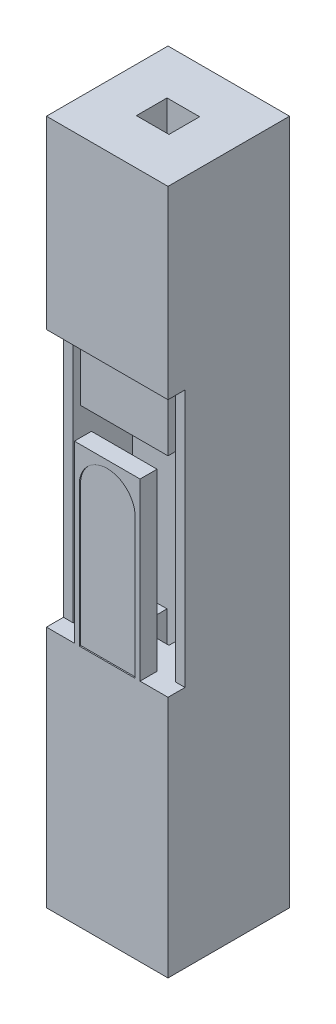
SolidWorks part; units mm, degrees
other "Camera1"
material "Nylon 101"
ref_plane "Front Plane" through (0, 0, 0) normal (0, 0, 1) x (1, 0, 0)
ref_plane "Top Plane" through (0, 0, 0) normal (0, 1, 0) x (1, 0, 0)
ref_plane "Right Plane" through (0, 0, 0) normal (1, 0, 0) x (0, 0, -1)
sketch "Sketch2" plane through (0, 0, 0) normal (0, 1, 0) x (1, 0, 0)
  line L1 (-1.25, -1.25) -> (1.25, -1.25)
  line L2 (-1.25, -1.25) -> (-1.25, 1.25)
  line L3 (-1.25, 1.25) -> (1.25, 1.25)
  line L4 (1.25, -1.25) -> (1.25, 1.25)
  line L5 (-1.25, -1.25) -> (1.25, 1.25) construction
  line L6 (-1.25, 1.25) -> (1.25, -1.25) construction
  point P0 (0, 0)
  dimension "D1" = 2.5
extrude "Boss-Extrude1" add sketch "Sketch2" along normal mid plane 14.1
sketch "Sketch3" plane through (0, 7.05, 0) normal (0, 1, 0) x (1, 0, 0)
  line L1 (0.335, -0.315) -> (-0.335, -0.315)
  line L2 (0.335, -0.315) -> (0.335, 0.315)
  line L3 (0.335, 0.315) -> (-0.335, 0.315)
  line L4 (-0.335, -0.315) -> (-0.335, 0.315)
  line L5 (0.335, -0.315) -> (-0.335, 0.315) construction
  line L6 (0.335, 0.315) -> (-0.335, -0.315) construction
  point P0 (0, 0)
  dimension "D1" = 0.63
  dimension "D2" = 0.67
extrude "Pinhole" cut sketch "Sketch3" against normal up to next
sketch "Sketch4" plane through (0, 0, 1.25) normal (0, 0, 1) x (1, 0, 0)
  line L0 (-1.25, 7.05) -> (-1.25, -7.05) construction
  line L1 (-1.25, 3.25) -> (1.25, 3.25)
  line L2 (-1.25, 3.25) -> (-1.25, -2.05)
  line L3 (-1.25, -2.05) -> (-0.675, -2.05)
  line L4 (1.25, 3.25) -> (1.25, -2.05)
  line L5 (0.675, -2.05) -> (1.25, -2.05)
  line L6 (-0.675, -2.05) -> (0.675, -2.05) construction
  line L7 (1.25, 7.05) -> (1.25, -7.05) construction
  line L8 (-1.25, 7.05) -> (1.25, 7.05) construction
  line L9 (-1.25, -7.05) -> (1.25, -7.05) construction
  line L10 (-0.675, -2.05) -> (-0.675, 1.55)
  line L11 (-0.675, 1.55) -> (0.675, 1.55)
  line L12 (0.675, -2.05) -> (0.675, 1.55)
  dimension "D1" = 3.8
  dimension "D2" = 5
  dimension "D3" = 1.35
  dimension "D4" = 3.6
extrude "Cut-Extrude2" cut sketch "Sketch4" against normal blind 0.35
sketch "Sketch5" plane through (0, 0, 0.9) normal (0, 0, 1) x (1, 0, 0)
  line L0 (-1.25, 7.05) -> (1.25, 7.05) construction
  line L1 (-1.05, 3.25) -> (1.05, 3.25)
  line L2 (-1.05, 3.25) -> (-1.05, -2.05)
  line L3 (-1.05, -2.05) -> (1.05, -2.05)
  line L4 (1.05, 3.25) -> (1.05, -2.05)
  line L5 (-1.05, 3.25) -> (1.05, -2.05) construction
  line L6 (-1.05, -2.05) -> (1.05, 3.25) construction
  line L7 (0.675, -2.05) -> (1.25, -2.05) construction
  line L8 (-1.25, 3.25) -> (-1.25, -2.05) construction
  line L9 (1.25, 3.25) -> (-1.25, 3.25) construction
  point P4 (0, 0.6)
  point P5 (0, 3.25)
  point P8 (0, 7.05)
  dimension "D1" = 0.2
extrude "Cut-Extrude3" cut sketch "Sketch5" against normal up to surface (1.215 mm away) up to face at (0, 0, -0.315)
sketch "Sketch6" plane through (0, 0, 1.25) normal (0, 0, 1) x (1, 0, 0)
  line L0 (-0.575, -2.05) -> (-0.575, 0.825)
  line L1 (-0.675, -2.05) -> (-0.675, 1.55) construction
  line L2 (-0.6925, -2.05) -> (0.6925, -2.05)
  line L3 (-1.05, -2.05) -> (-0.335, -2.05) construction
  line L4 (0.335, -2.05) -> (1.05, -2.05) construction
  line L5 (0, 1.55) -> (0, -2.05) construction
  line L6 (-0.675, 1.55) -> (0.675, 1.55) construction
  line L7 (0.575, -2.05) -> (0.575, 0.825)
  arc A0 (-0.575, 0.825) -> (0.575, 0.825) centre (0, 0.825) cw
  point P17 (0, 1.4)
  dimension "D2" = 0.15
  dimension "D1" = 0.1
extrude "Cut-Extrude5" cut sketch "Sketch6" against normal blind 0.025 contours L5 A0 L0 L2 | A0 L5 L2 L7
sketch "Sketch7" plane through (0, -7.05, 0) normal (0, -1, 0) x (1, 0, 0)
  line L0 (-1.25, -1.25) -> (-1.25, 1.25) construction
  line L1 (1.05, -1.05) -> (-1.05, -1.05)
  line L2 (1.05, -1.05) -> (1.05, 1.05)
  line L3 (1.05, 1.05) -> (-1.05, 1.05)
  line L4 (-1.05, -1.05) -> (-1.05, 1.05)
  line L5 (1.05, -1.05) -> (-1.05, 1.05) construction
  line L6 (1.05, 1.05) -> (-1.05, -1.05) construction
  point P0 (0, 0)
  dimension "D1" = 0.2
extrude "Cut-Extrude6" cut sketch "Sketch7" against normal blind 4
sketch "Sketch8" [suppressed] plane through (0, -3.05, 0) normal (0, -1, 0) x (1, 0, 0)
  circle A0 centre (0, 0) radius 0.45
  circle A1 centre (0, 0) radius 0.55
  dimension "D1" = 0.9
  dimension "D2" = 0.1
extrude "Wire hole" [suppressed] add sketch "Sketch8" along normal blind 3
sketch "Sketch9" plane through (0, 0, -0.315) normal (0, 0, 1) x (1, 0, 0)
  line L1 (-0.9, 2.9) -> (-0.75, 2.9)
  line L2 (-0.9, 2.9) -> (-0.9, 1.9)
  line L3 (-0.9, 1.9) -> (-0.75, 1.9)
  line L4 (0.9, 2.9) -> (0.9, 1.9)
  line L5 (0.75, 2.9) -> (-0.75, 2.9) construction
  line L6 (0.9, 2.9) -> (0.75, 2.9)
  line L7 (-0.335, 3.25) -> (0.335, 3.25) construction
  line L8 (-0.75, 2.9) -> (-0.75, 1.9)
  line L9 (0, 2.9) -> (0, 1.9) construction
  line L10 (0.75, 2.9) -> (0.75, 1.9)
  line L11 (-1.05, 3.25) -> (-1.05, -2.05) construction
  line L12 (0, 3.25) -> (0, 2.9) construction
  line L13 (0.75, 1.9) -> (-0.75, 1.9) construction
  line L14 (0.75, 1.9) -> (0.9, 1.9)
  point P4 (0, 2.4)
  point P23 (0, 2.9)
  point P24 (0, 1.9)
  dimension "D1" = 1
  dimension "D2" = 0.15
  dimension "D3" = 0.15
  dimension "D4" = 0.85
extrude "Holder-1" add sketch "Sketch9" along normal offset from surface (1.065 mm away) 0.15 up to face at (0, -0.25, 0.9)
sketch "Sketch10" plane through (0, 0, 0.75) normal (0, 0, 1) x (1, 0, 0)
  line L1 (-0.9, 2.9) -> (0.9, 2.9)
  line L2 (-0.9, 2.9) -> (-0.9, 1.9)
  line L3 (-0.9, 1.9) -> (0.9, 1.9)
  line L4 (0.9, 2.9) -> (0.9, 1.9)
  line L5 (-0.9, 2.9) -> (0.9, 1.9) construction
  line L6 (-0.9, 1.9) -> (0.9, 2.9) construction
  point P4 (0, 2.4)
extrude "Holder-2" add sketch "Sketch10" along normal blind 0.15
ref_plane "Snap plane" through (0, 6.05, 0) normal (0, 1, 0) x (1, 0, 0)
